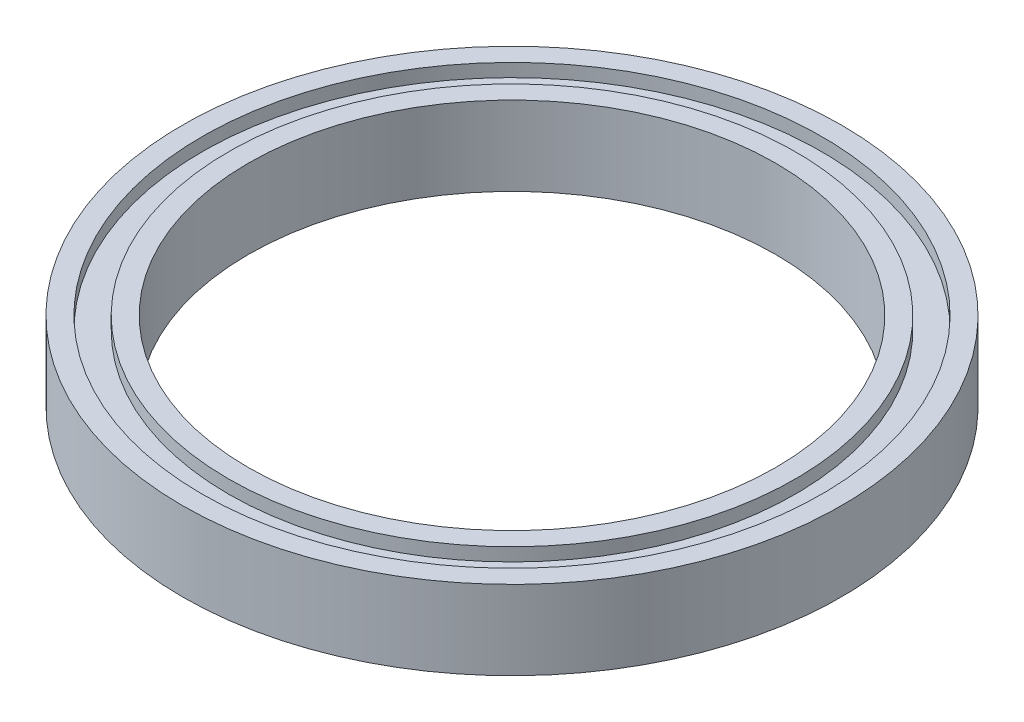
SolidWorks part; units mm, degrees
ref_plane "Front Plane" through (0, 0, 0) normal (0, 0, 1) x (1, 0, 0)
ref_plane "Top Plane" through (0, 0, 0) normal (0, 1, 0) x (1, 0, 0)
ref_plane "Right Plane" through (0, 0, 0) normal (1, 0, 0) x (0, 0, -1)
sketch "Sketch1" plane through (0, 0, 0) normal (0, 1, 0) x (1, 0, 0)
  circle A0 centre (0, 0) radius 20
  circle A1 centre (0, 0) radius 25
  dimension "D1" = 50
  dimension "D2" = 40
extrude "Boss-Extrude1" add sketch "Sketch1" along normal blind 6
sketch "Sketch2" plane through (0, 6, 0) normal (0, 1, 0) x (1, 0, 0)
  circle A2 centre (0, 0) radius 23.5
  circle A3 centre (0, 0) radius 23.5
  circle A5 centre (0, 0) radius 21.5
  circle A6 centre (0, 0) radius 21.5
  dimension "D1" = 1.5
  dimension "D2" = 1.5
extrude "Cut-Extrude1" cut sketch "Sketch2" against normal blind 1
sketch "Sketch3" plane through (0, 0, 0) normal (0, -1, 0) x (1, 0, 0)
  circle A2 centre (0, 0) radius 23
  circle A3 centre (0, 0) radius 23
  circle A5 centre (0, 0) radius 22
  circle A6 centre (0, 0) radius 22
  dimension "D1" = 2
  dimension "D2" = 2
extrude "Cut-Extrude2" cut sketch "Sketch3" against normal blind 1
